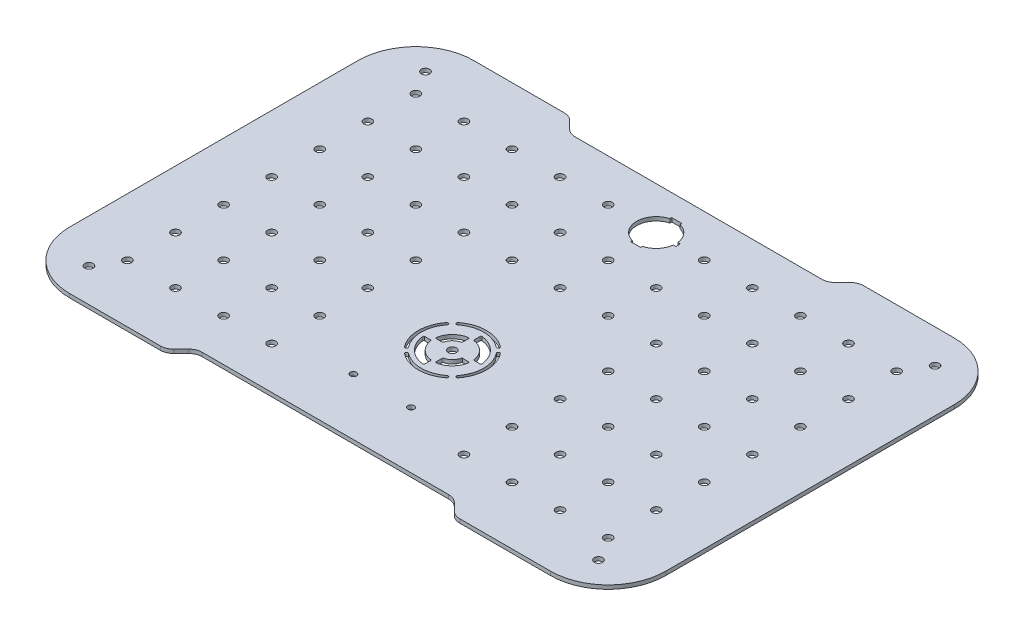
SolidWorks part; units mm, degrees
ref_plane "Front Plane" through (0, 0, 0) normal (0, 0, 1) x (1, 0, 0)
ref_plane "Top Plane" through (0, 0, 0) normal (0, 1, 0) x (1, 0, 0)
ref_plane "Right Plane" through (0, 0, 0) normal (1, 0, 0) x (0, 0, -1)
sketch "Sketch1" plane through (0, 0, 0) normal (0, 1, 0) x (1, 0, 0)
  line L0 (0, 105) -> (0, 0) construction
  line L5 (125, -105) -> (-125, -105)
  line L6 (155, -75) -> (155, 75)
  line L7 (125, 105) -> (-125, 105)
  line L8 (-155, -75) -> (-155, 75)
  line L9 (0, 0) -> (155, 0) construction
  arc A4 (125, 105) -> (155, 75) centre (125, 75) cw
  arc A5 (155, -75) -> (125, -105) centre (125, -75) cw
  arc A6 (-125, -105) -> (-155, -75) centre (-125, -75) cw
  arc A7 (-155, 75) -> (-125, 105) centre (-125, 75) cw
  point P0 (0, 0)
  dimension "D3" = 210
  dimension "D1" = 30
  dimension "D2" = 310
ref_plane "Plane1" through (0, -40, 0) normal (0, 1, 0) x (1, 0, 0)
sketch "Sketch8" plane through (0, 0, 0) normal (0, 1, 0) x (1, 0, 0)
  line L1 (-132.5, -87.5) -> (132.5, -87.5) construction
  line L2 (-132.5, -87.5) -> (-132.5, 87.5) construction
  line L3 (-132.5, 87.5) -> (132.5, 87.5) construction
  line L4 (132.5, -87.5) -> (132.5, 87.5) construction
  line L5 (-132.5, -87.5) -> (132.5, 87.5) construction
  line L6 (-132.5, 87.5) -> (132.5, -87.5) construction
  circle A0 centre (-132.5, 87.5) radius 2.15
  circle A1 centre (132.5, 87.5) radius 2.15
  circle A2 centre (-132.5, -87.5) radius 2.15
  circle A3 centre (132.5, -87.5) radius 2.15
  point P0 (0, 0)
  dimension "D1" = 4.3
  dimension "D2" = 265
  dimension "D3" = 175
extrude "Boss-Extrude1" add sketch "Sketch1" against normal blind 2
extrude "Cut-Extrude11" cut sketch "Sketch8" against normal through all
sketch "Sketch9" plane through (0, 0, 0) normal (0, 1, 0) x (1, 0, 0)
  line L0 (-75, -105) -> (-67, -97)
  line L1 (-125, -105) -> (125, -105) construction
  line L2 (-67, -97) -> (67, -97)
  line L3 (67, -97) -> (75, -105)
  line L4 (75, -105) -> (-75, -105)
  line L5 (0, -105) -> (0, -97) construction
  line L6 (0, -97) -> (0, 0) construction
  dimension "D1" = 150
  dimension "D2" = 135
  dimension "D3" = 8
extrude "Cut-Extrude12" cut sketch "Sketch9" against normal through all
mirror "Mirror2" about plane through (0, 0, 0) normal (0, 0, 1) of "Cut-Extrude12"
fillet "Fillet1" radius 7 8 edges at (-67, -1, 97) (67, -1, 97) (75, -1, 105) (-75, -1, 105) (-75, -1, -105) (75, -1, -105) (-67, -1, -97) (67, -1, -97)
sketch "Sketch11" plane through (0, 0, 0) normal (0, 1, 0) x (1, 0, 0)
  line L0 (0, 0) -> (0, -31) construction
  circle A0 centre (0, -31) radius 2.15
  dimension "D2" = 4.3
  dimension "D1" = 31
extrude "Cut-Extrude14" cut sketch "Sketch11" against normal through all
sketch "Sketch10" plane through (0, 0, 0) normal (0, 1, 0) x (1, 0, 0)
  line L0 (0, 0) -> (0, -31) construction
  line L1 (125, -75) -> (-125, -75) construction
  line L2 (125, -75) -> (125, 75) construction
  line L3 (125, 75) -> (-125, 75) construction
  line L4 (-125, -75) -> (-125, 75) construction
  line L5 (125, -75) -> (-125, 75) construction
  line L6 (125, 75) -> (-125, -75) construction
  arc A0 (-125, 105) -> (-155, 75) centre (-125, 75) ccw construction
  circle A1 centre (-125, 75) radius 2.15
  point P0 (0, 0)
  dimension "D3" = 4.3
  dimension "D1" = 250
  dimension "D2" = 150
extrude "Cut-Extrude13" cut sketch "Sketch10" against normal through all
pattern_linear "LPattern1" count 7 spacing 25 along (0, 0, 1) count 11 spacing 25 along (1, 0, 0) skipping (3, 4), (3, 5), (3, 6), (4, 4), (4, 5), (4, 6), (5, 4), (5, 5), (5, 6), (6, 4), (6, 5), (6, 6) of "Cut-Extrude13"
sketch "Sketch15" plane through (0, 0, 0) normal (0, 1, 0) x (1, 0, 0)
  line L0 (1, -17.0501) -> (1, -21.0501)
  line L1 (-1, -40.9499) -> (-1, -44.9499)
  line L2 (13.9499, -30) -> (9.9499, -30)
  line L3 (-13.9499, -32) -> (-9.9499, -32)
  arc A0 (-13.9499, -32) -> (-1, -44.9499) centre (0, -31) ccw
  arc A1 (-9.9499, -32) -> (-1, -40.9499) centre (0, -31) ccw
  arc A2 (9.9499, -30) -> (1, -21.0501) centre (0, -31) ccw
  arc A3 (13.9499, -30) -> (1, -17.0501) centre (0, -31) ccw
  circle A4 centre (0, -31) radius 2.15 construction
  dimension "D1" = 10
  dimension "D2" = 4
  dimension "D3" = 1
  dimension "D4" = 1
  dimension "D5" = 1
  dimension "D6" = 1
extrude "Cut-Extrude18" cut sketch "Sketch15" against normal through all
sketch "Sketch16" plane through (0, 0, 0) normal (0, 1, 0) x (1, 0, 0)
  line L0 (-1, -21.0501) -> (-1, -25.0501)
  line L1 (-5.9499, -30) -> (-9.9499, -30)
  line L2 (1, -36.9499) -> (1, -40.9499)
  line L3 (5.9499, -32) -> (9.9499, -32)
  line L4 (1, -17.0501) -> (1, -21.0501) construction
  arc A0 (-1, -25.0501) -> (-5.9499, -30) centre (0, -31) ccw
  arc A1 (-1, -21.0501) -> (-9.9499, -30) centre (0, -31) ccw
  arc A2 (1, -36.9499) -> (5.9499, -32) centre (0, -31) ccw
  arc A3 (1, -40.9499) -> (9.9499, -32) centre (0, -31) ccw
  arc A4 (9.9499, -30) -> (1, -21.0501) centre (0, -31) ccw construction
  circle A5 centre (0, -31) radius 2.15 construction
  dimension "D3" = 1
  dimension "D1" = 1
  dimension "D2" = 1
  dimension "D4" = 1
extrude "Cut-Extrude19" cut sketch "Sketch16" against normal through all
sketch "Sketch17" plane through (0, 0, 0) normal (0, 1, 0) x (1, 0, 0)
  line L0 (0, -14) -> (0, -31) construction
  line L1 (0, -31) -> (10.4662, -17.6038) construction
  arc A0 (-10.4662, -17.6038) -> (10.4662, -17.6038) centre (0, -31) cw construction
  arc A1 (10.928, -17.0128) -> (-10.928, -17.0128) centre (0, -31) ccw
  arc A2 (10.0045, -18.1948) -> (-10.0045, -18.1948) centre (0, -31) ccw
  arc A3 (10.0045, -18.1948) -> (10.928, -17.0128) centre (10.4662, -17.6038) ccw
  arc A4 (-10.928, -17.0128) -> (-10.0045, -18.1948) centre (-10.4662, -17.6038) ccw
  point P4 (0, -14)
  dimension "D1" = 17
  dimension "D2" = 1.5
  dimension "D3" = 38
extrude "Cut-Extrude20" cut sketch "Sketch17" against normal through all
pattern_circular "CirPattern4" count 4 over 360 about axis through (0, 0, 31) along (0, 1, 0) of "Cut-Extrude20"
fillet "Fillet2" radius 0.5 16 edges at (-5.9499, -1, 30) (-9.9499, -1, 30) (-13.9499, -1, 32) (-9.9499, -1, 32) (-1, -1, 44.9499) (-1, -1, 40.9499) (1, -1, 40.9499) (1, -1, 36.9499) (9.9499, -1, 32) (5.9499, -1, 32) (13.9499, -1, 30) (9.9499, -1, 30) (-1, -1, 25.0501) (-1, -1, 21.0501) (1, -1, 21.0501) (1, -1, 17.0501)
sketch "Sketch18" plane through (0, 0, 0) normal (0, 1, 0) x (1, 0, 0)
  line L0 (-15, -67.5) -> (15, -67.5) construction
  line L1 (0, -67.5) -> (0, -97) construction
  line L2 (64.1005, -97) -> (-64.1005, -97) construction
  circle A0 centre (15, -67.5) radius 1.65
  circle A1 centre (-15, -67.5) radius 1.65
  dimension "D3" = 3.3
  dimension "D1" = 29.5
  dimension "D2" = 30
extrude "Cut-Extrude21" cut sketch "Sketch18" against normal through all
sketch "Sketch19" plane through (0, 0, 0) normal (0, 1, 0) x (1, 0, 0)
  circle A0 centre (0, 75) radius 10.15
  dimension "D1" = 20.3
extrude "Cut-Extrude22" cut sketch "Sketch19" against normal through all
sketch "Sketch20" plane through (0, 0, 0) normal (0, 1, 0) x (1, 0, 0)
  line L0 (8.9, 75) -> (0, 75) construction
  line L1 (11.4, 73.85) -> (8.9, 73.85)
  line L2 (11.4, 73.85) -> (11.4, 76.15)
  line L3 (11.4, 76.15) -> (8.9, 76.15)
  line L4 (8.9, 73.85) -> (8.9, 76.15)
  line L5 (11.4, 73.85) -> (8.9, 76.15) construction
  line L6 (11.4, 76.15) -> (8.9, 73.85) construction
  circle A0 centre (0, 75) radius 10.15 construction
  circle A1 centre (0, 75) radius 11.5 construction
  point P0 (10.15, 75)
  dimension "D3" = 23
  dimension "D1" = 2.3
  dimension "D2" = 2.5
extrude "Cut-Extrude23" cut sketch "Sketch20" against normal through all
sketch "Sketch21" plane through (0, 0, 0) normal (0, 1, 0) x (1, 0, 0)
  line L1 (-2.65, 64.25) -> (2.65, 64.25)
  line L2 (-2.65, 64.25) -> (-2.65, 85.75)
  line L3 (-2.65, 85.75) -> (2.65, 85.75)
  line L4 (2.65, 64.25) -> (2.65, 85.75)
  line L5 (-2.65, 64.25) -> (2.65, 85.75) construction
  line L6 (-2.65, 85.75) -> (2.65, 64.25) construction
  circle A0 centre (0, 75) radius 11.5 construction
  point P0 (0, 75)
  dimension "D3" = 23
  dimension "D1" = 5.3
  dimension "D2" = 21.5
extrude "Cut-Extrude24" cut sketch "Sketch21" against normal through all
